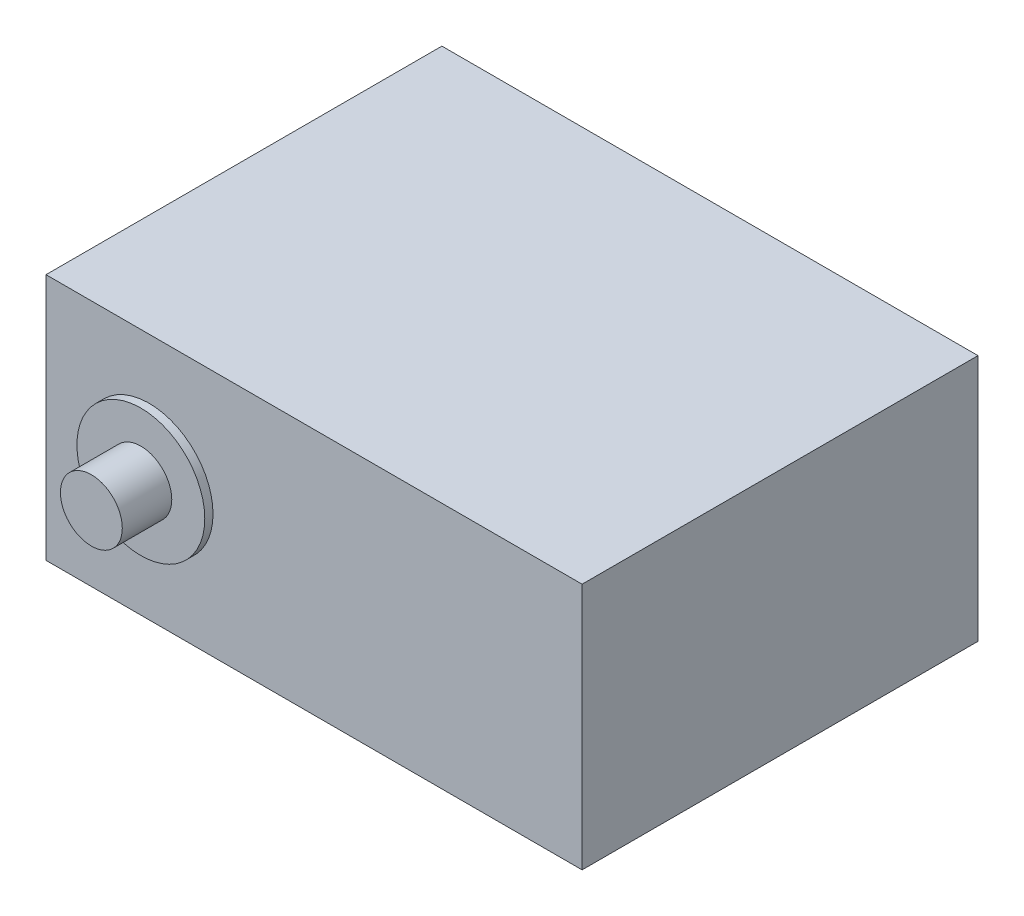
SolidWorks part; units mm, degrees
ref_plane "Front Plane" through (0, 0, 0) normal (0, 0, 1) x (1, 0, 0)
ref_plane "Top Plane" through (0, 0, 0) normal (0, 1, 0) x (1, 0, 0)
ref_plane "Right Plane" through (0, 0, 0) normal (1, 0, 0) x (0, 0, -1)
sketch "Sketch2" plane through (0, 0, 0) normal (0, 0, 1) x (1, 0, 0)
  line L0 (-24.1429, 16.3571) -> (-24.1429, -13.6429)
  line L1 (-24.1429, -13.6429) -> (40.8571, -13.6429)
  line L2 (40.8571, -13.6429) -> (40.8571, 16.3571)
  line L3 (-24.1429, 16.3571) -> (40.8571, 16.3571)
  dimension "D1" = 30
  dimension "65" = 65
extrude "Boss-Extrude1" add sketch "Sketch2" along normal blind 48
sketch "Sketch3" plane through (0, 0, 48) normal (0, 0, 1) x (1, 0, 0)
  line L0 (-24.1429, 16.3571) -> (-24.1429, -13.6429) construction
  line L1 (40.8571, 16.3571) -> (-24.1429, 16.3571) construction
  circle A0 centre (-11.6429, 1.3571) radius 3.75
  dimension "D4" = 7.5
  dimension "D1" = 12.5
  dimension "D2" = 15
extrude "Boss-Extrude2" add sketch "Sketch3" along normal blind 7
sketch "Sketch4" plane through (0, 0, 48) normal (0, 0, 1) x (1, 0, 0)
  circle A0 centre (-11.6429, 1.3571) radius 7.75
  dimension "D1" = 15.5
extrude "Boss-Extrude3" add sketch "Sketch4" along normal blind 1
sketch "Sketch5" plane through (0, 0, 0) normal (0, 0, -1) x (-1, 0, 0)
  line L0 (-40.8571, 16.3571) -> (24.1429, 16.3571) construction
  line L2 (-40.8571, -13.6429) -> (-40.8571, 16.3571) construction
  circle A0 centre (11.6429, 1.3571) radius 3
  point P6 (-40.8571, 3.0976)
  dimension "D3" = 6
  dimension "D1" = 15
  dimension "D2" = 52.5
extrude "Boss-Extrude6" add sketch "Sketch5" along normal blind 7
sketch "Sketch7" plane through (0, 0, 0) normal (0, 0, -1) x (-1, 0, 0)
  circle A0 centre (11.6429, 1.3571) radius 7.75
  dimension "D1" = 15.5
extrude "Boss-Extrude7" add sketch "Sketch7" along normal blind 1
sketch "Sketch8" plane through (-24.1429, 0, 0) normal (-1, 0, 0) x (0, 0, 1)
  line L0 (48, 16.3571) -> (0, 16.3571) construction
  line L1 (6.5, 4.3571) -> (10.5, 4.3571)
  line L2 (6.5, 4.3571) -> (6.5, -1.6429)
  line L3 (6.5, -1.6429) -> (10.5, -1.6429)
  line L4 (10.5, 4.3571) -> (10.5, -1.6429)
  line L5 (6.5, 4.3571) -> (10.5, -1.6429) construction
  line L6 (6.5, -1.6429) -> (10.5, 4.3571) construction
  line L7 (0, 9.1071) -> (0, -6.3929) construction
  point P0 (8.5, 1.3571)
  dimension "D1" = 15
  dimension "D2" = 8.5
  dimension "D3" = 4
  dimension "D4" = 6
extrude "Boss-Extrude8" add sketch "Sketch8" along normal blind 5.5
